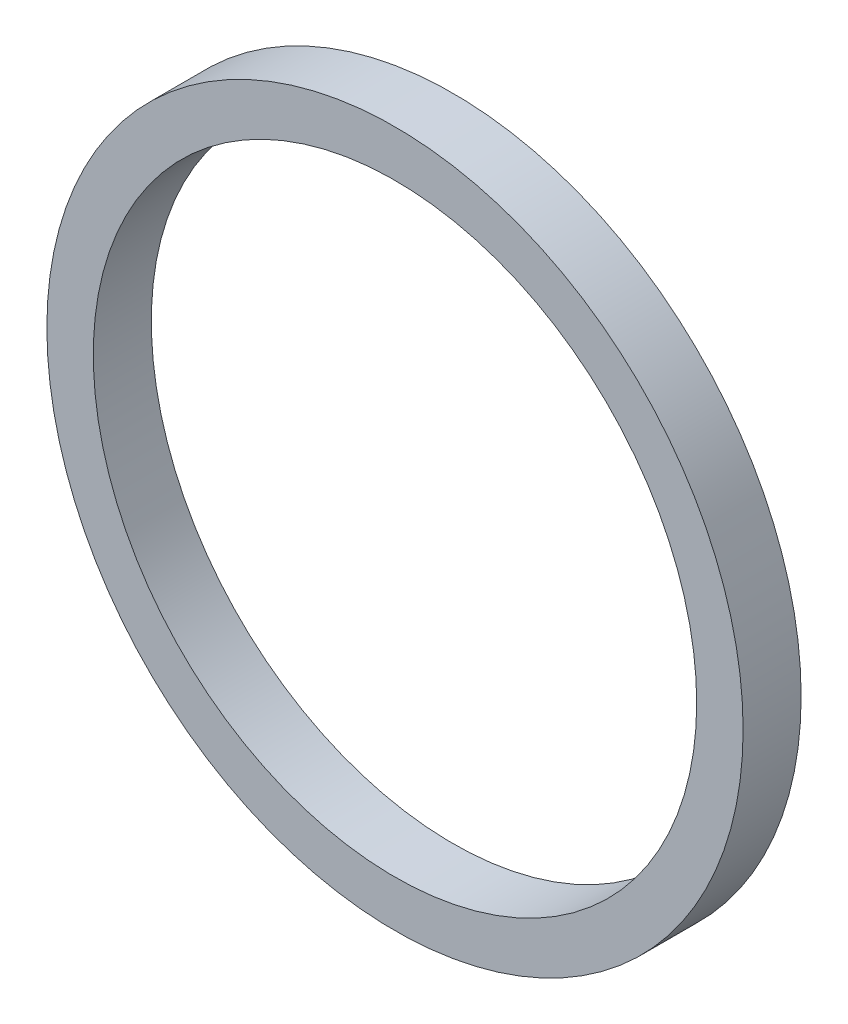
SolidWorks part; units mm, degrees
ref_plane "Front Plane" through (0, 0, 0) normal (0, 0, 1) x (1, 0, 0)
ref_plane "Top Plane" through (0, 0, 0) normal (0, 1, 0) x (1, 0, 0)
ref_plane "Right Plane" through (0, 0, 0) normal (1, 0, 0) x (0, 0, -1)
sketch "Sketch1" plane through (0, 0, 0) normal (0, 0, 1) x (1, 0, 0)
  circle A0 centre (0, 0) radius 16.51
  circle A1 centre (0, 0) radius 19.05
  dimension "D1" = 38.1
  dimension "D2" = 2.54
extrude "Boss-Extrude1" add sketch "Sketch1" along normal blind 3.175
